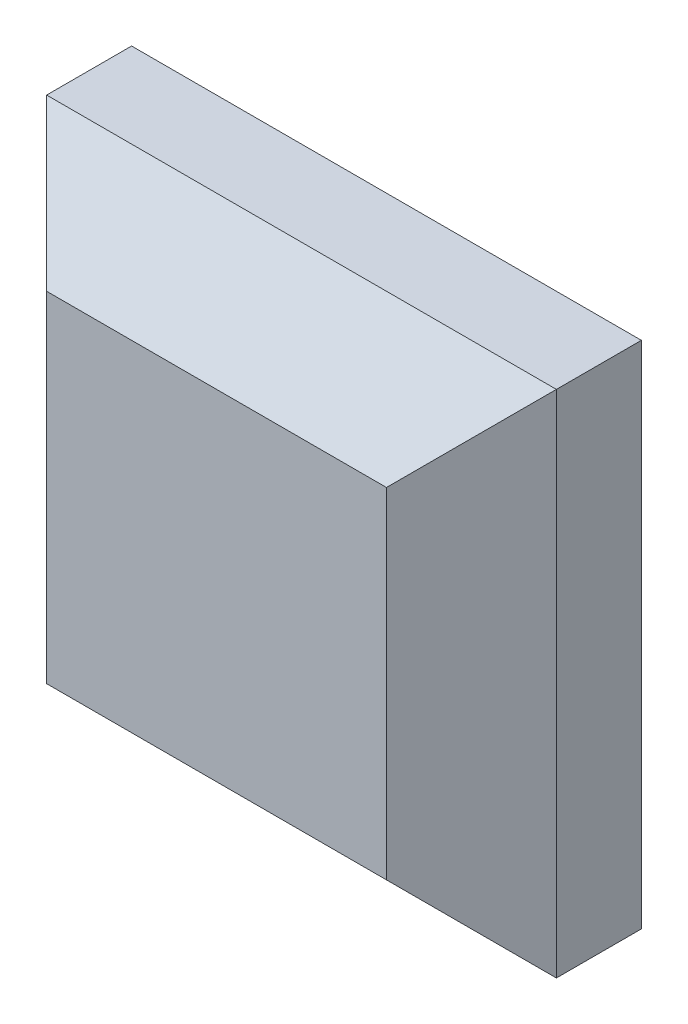
SolidWorks part; units mm, degrees
ref_plane "Top Plane" through (0, 0, 0) normal (0, 0, 1) x (1, 0, 0)
ref_plane "Right Plane" through (0, 0, 0) normal (0, 1, 0) x (1, 0, 0)
ref_plane "Front Plane" through (0, 0, 0) normal (1, 0, 0) x (0, 0, -1)
sketch "Sketch1" plane through (0, 0, 0) normal (0, 0, 1) x (1, 0, 0)
  line L1 (-15, -15) -> (15, -15)
  line L2 (-15, -15) -> (-15, 15)
  line L3 (-15, 15) -> (15, 15)
  line L4 (15, -15) -> (15, 15)
  line L5 (-15, -15) -> (15, 15) construction
  line L6 (-15, 15) -> (15, -15) construction
  point P0 (0, 0)
extrude "Boss-Extrude1" add sketch "Sketch1" along normal blind 10
chamfer "Chamfer1" distance 5 angle 45 4 edges at (0, -15, 10) (-15, 0, 10) (0, 15, 10) (15, 0, 10)
shell "Shell1" thickness 2
sketch "Sketch2" plane through (0, 0, 0) normal (0, 0, -1) x (-1, 0, 0)
  line L1 (13, 2.5) -> (2.5, 2.5)
  line L2 (13, 2.5) -> (13, -2.5)
  line L3 (13, -2.5) -> (2.5, -2.5)
  line L4 (-13, 2.5) -> (-13, -2.5)
  line L5 (13, 2.5) -> (-13, -2.5) construction
  line L6 (13, -2.5) -> (-13, 2.5) construction
  line L8 (2.5, 13) -> (-2.5, 13)
  line L9 (2.5, 13) -> (2.5, 2.5)
  line L10 (2.5, -13) -> (-2.5, -13)
  line L11 (-2.5, 13) -> (-2.5, 2.5)
  line L12 (2.5, 13) -> (-2.5, -13) construction
  line L13 (2.5, -13) -> (-2.5, 13) construction
  line L14 (-13, -13) -> (-13, 13) construction
  line L15 (13, -13) -> (-13, -13) construction
  line L16 (-2.5, -2.5) -> (-13, -2.5)
  line L17 (2.5, -2.5) -> (2.5, -13)
  line L18 (-2.5, 2.5) -> (-13, 2.5)
  line L19 (-2.5, -2.5) -> (-2.5, -13)
  point P0 (0, 0)
  point P6 (-13, -1.8435)
  point P8 (0, 0)
  point P13 (-2.6586, -13)
  point P16 (0, 0)
  dimension "D1" = 5
extrude "Boss-Extrude2" add sketch "Sketch2" against normal up to next
